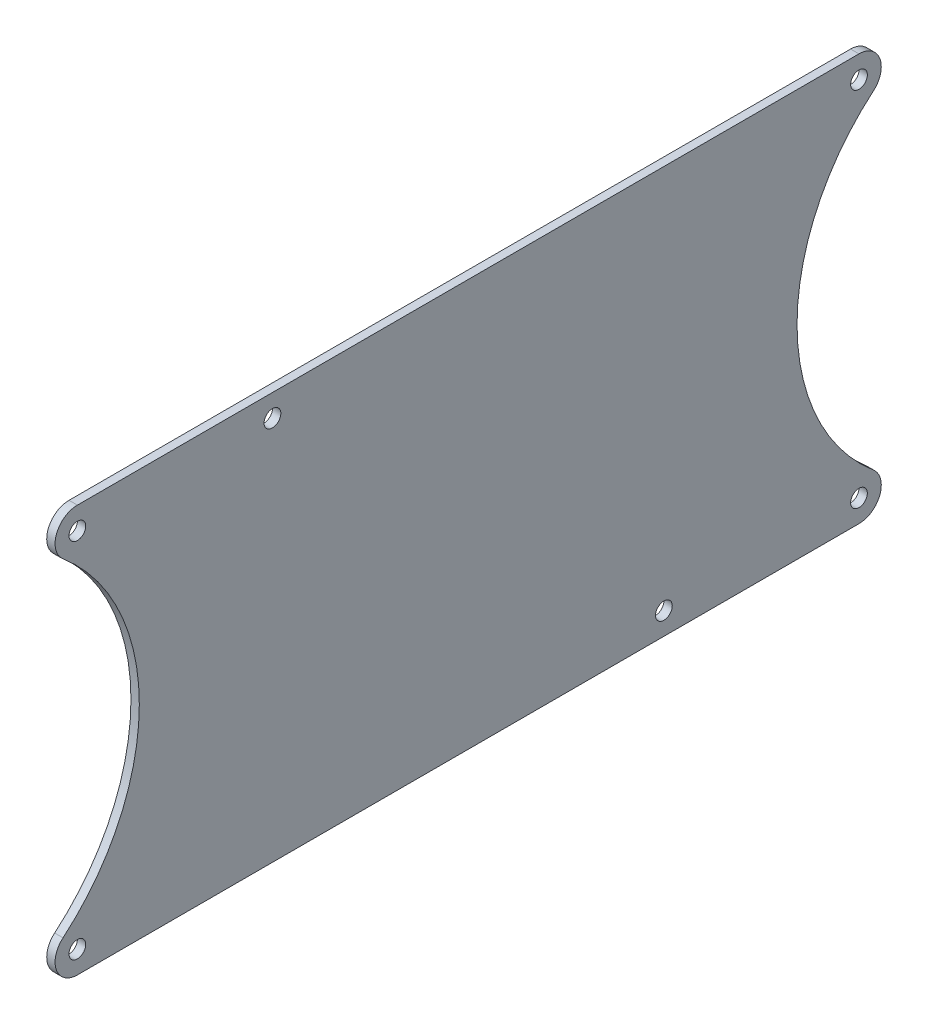
SolidWorks part; units mm, degrees
material "Hexcel AS4C (3000 Filaments)"
ref_plane "Front Plane" through (0, 0, 0) normal (0, 0, 1) x (1, 0, 0)
ref_plane "Top Plane" through (0, 0, 0) normal (0, 1, 0) x (1, 0, 0)
ref_plane "Right Plane" through (0, 0, 0) normal (1, 0, 0) x (0, 0, -1)
sketch "Sketch1" plane through (0, 0, 0) normal (1, 0, 0) x (0, 0, -1)
  line L0 (-18.6408, 41.2157) -> (176.3592, 41.2157) construction
  line L1 (-18.6408, -33.7843) -> (176.3592, -33.7843) construction
  line L2 (-18.6408, 40.2157) -> (176.3592, 40.2157)
  line L3 (-18.6408, -34.7843) -> (176.3592, -34.7843)
  line L4 (-18.6408, 42.2157) -> (176.3592, 42.2157)
  line L5 (-18.6408, -32.7843) -> (176.3592, -32.7843)
  circle A0 centre (-18.6408, 3.7157) radius 37.5 construction
  circle A1 centre (176.3592, 3.7157) radius 37.5 construction
  circle A2 centre (-18.6408, 3.7157) radius 38.5
  circle A3 centre (176.3592, 3.7157) radius 38.5
  circle A4 centre (-18.6408, 3.7157) radius 36.5
  circle A5 centre (176.3592, 3.7157) radius 36.5
  dimension "D1" = 75
  dimension "D2" = 75
  dimension "D3" = 195
  dimension "D4" = 1
  dimension "D5" = 1
extrude "Boss-Extrude1" add sketch "Sketch1" along normal blind 1.5 contours A1 L0 A0 L1 | A3 L2 A2 L5
fillet "Fillet1" radius 4 4 edges at (0.75, 40.2157, -164.1118) (0.75, -32.7843, -164.1118) (0.75, -32.7843, 6.3933) (0.75, 40.2157, 6.3933)
hole_wizard "Ø3.0mm Dowel Hole2" positions "Sketch7" profile "Sketch6" hole size "Ø3.0" standard "ISO"
sketch "Sketch7" plane through (1.5, 0, 0) normal (1, 0, 0) x (0, 0, -1)
  arc A3 (8.7453, 40.2157) -> (6.1678, 33.1569) centre (8.7453, 36.2157) ccw construction
  arc A4 (151.5506, 33.1569) -> (148.9731, 40.2157) centre (148.9731, 36.2157) ccw construction
  arc A5 (148.9731, -32.7843) -> (151.5506, -25.7255) centre (148.9731, -28.7843) ccw construction
  arc A6 (6.1678, -25.7255) -> (8.7453, -32.7843) centre (8.7453, -28.7843) ccw construction
  point P0 (8.7453, 36.2157)
  point P2 (148.9731, 36.2157)
  point P4 (148.9731, -28.7843)
  point P6 (8.7453, -28.7843)
  point P36 (43.7453, 36.2157)
  point P38 (113.9731, -28.7843)
  dimension "D1" = 35
  dimension "D2" = 35
sketch "Sketch6" plane through (1.5, 36.2157, -8.7453) normal (0, 1, 0) x (0, 0, -1)
  line L0 (0, 0) -> (0, 18.1913)
  line L1 (0, 18.1913) -> (1.5, 17.29)
  line L2 (1.5, 17.29) -> (1.5, 0)
  line L5 (1.5, 0) -> (0, 0)
  line L10 (0, 18.1913) -> (-1.5, 17.29) construction
  line L11 (0, -6.35) -> (0, 107.95) construction
  dimension "Hole Dia." = 3
  dimension "Hole Depth" = 17.29
  dimension "Drill Angle" = 118
